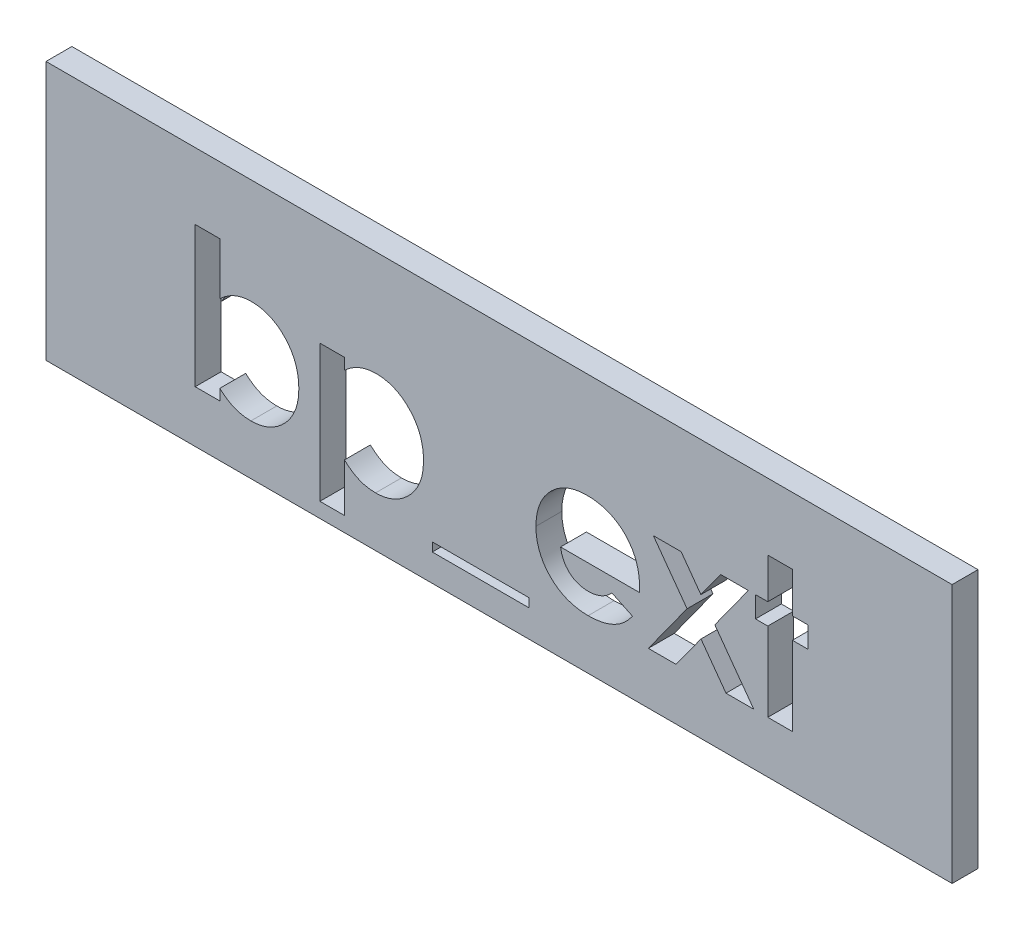
SolidWorks part; units mm, degrees
ref_plane "Plan de face" through (0, 0, 0) normal (0, 0, 1) x (1, 0, 0)
ref_plane "Plan de dessus" through (0, 0, 0) normal (0, 1, 0) x (1, 0, 0)
ref_plane "Plan de droite" through (0, 0, 0) normal (1, 0, 0) x (0, 0, -1)
sketch "Esquisse1" plane through (0, 0, 0) normal (0, 0, 1) x (1, 0, 0)
  line L1 (0, 0) -> (35, 0)
  line L2 (0, 0) -> (0, -10)
  line L3 (0, -10) -> (35, -10)
  line L4 (35, 0) -> (35, -10)
  dimension "D1" = 35
  dimension "D2" = 10
extrude "Boss.-Extru.1" add sketch "Esquisse1" along normal blind 1
sketch "Esquisse2" plane through (0, 0, 0) normal (0, 0, -1) x (-1, 0, 0)
  line L0 (-35, 0) -> (0, 0) construction
  line L1 (-35, -10) -> (-35, 0) construction
  line L2 (0, 0) -> (0, -10) construction
  circle A0 centre (-30, -5) radius 1
  circle A1 centre (-5, -5) radius 1
  dimension "D4" = 2
  dimension "D1" = 5
  dimension "D2" = 5
  dimension "D3" = 5
extrude "Boss.-Extru.2" add sketch "Esquisse2" along normal blind 3
chamfer "Chanfrein1" distance 0.5 angle 45 2 edges at (29, -5, -3) (4, -5, -3)
sketch "Esquisse3" plane through (0, 0, 1) normal (0, 0, 1) x (1, 0, 0)
  line L0 (5, -8) -> (30, -8) construction
  line L3 (0, -10) -> (35, -10) construction
  line L4 (0, 0) -> (0, -10) construction
  line L5 (35, -10) -> (35, 0) construction
  text T1 "<b>bp_ext</b>" font "Century Gothic" height in points 20
  point P12 (30, -8)
  dimension "D1" = 2
  dimension "D2" = 5
  dimension "D3" = 25
  dimension "D4" = 5
extrude "Enlèv. mat.-Extru.2" cut sketch "Esquisse3" against normal blind 1
